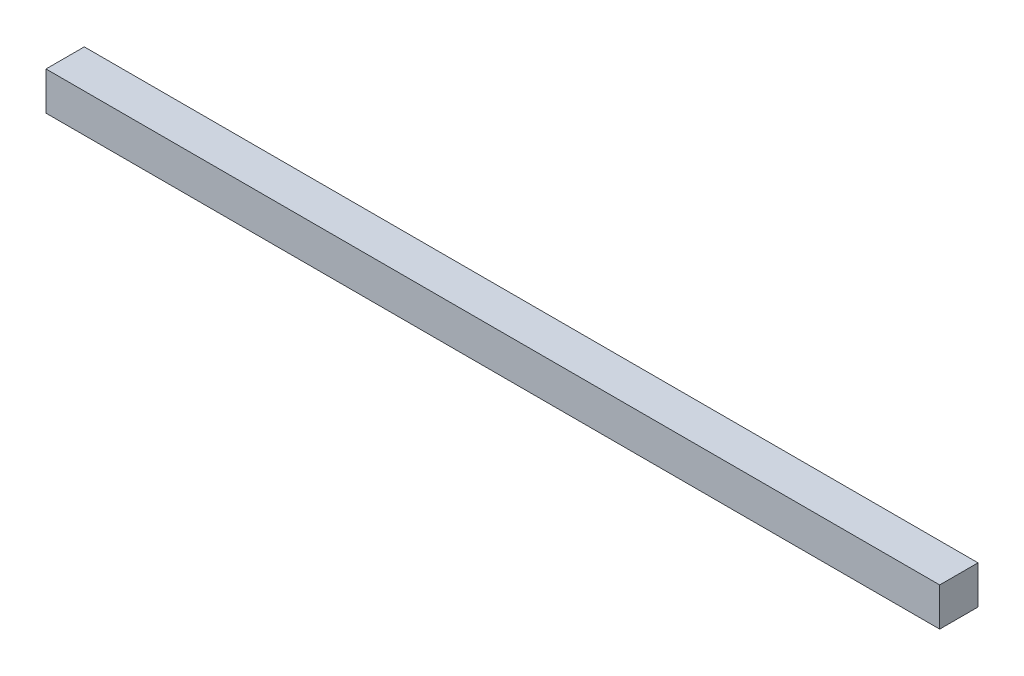
SolidWorks part; units mm, degrees
ref_plane "Front Plane" through (0, 0, 0) normal (0, 0, 1) x (1, 0, 0)
ref_plane "Top Plane" through (0, 0, 0) normal (0, 1, 0) x (1, 0, 0)
ref_plane "Right Plane" through (0, 0, 0) normal (1, 0, 0) x (0, 0, -1)
sketch "Sketch1" plane through (0, 0, 0) normal (0, 1, 0) x (1, 0, 0)
  line L1 (0, 0) -> (70, 0)
  line L2 (0, 0) -> (0, 3)
  line L3 (0, 3) -> (70, 3)
  line L4 (70, 0) -> (70, 3)
  dimension "D1" = 70
  dimension "D2" = 3
extrude "Boss-Extrude1" add sketch "Sketch1" along normal blind 3
